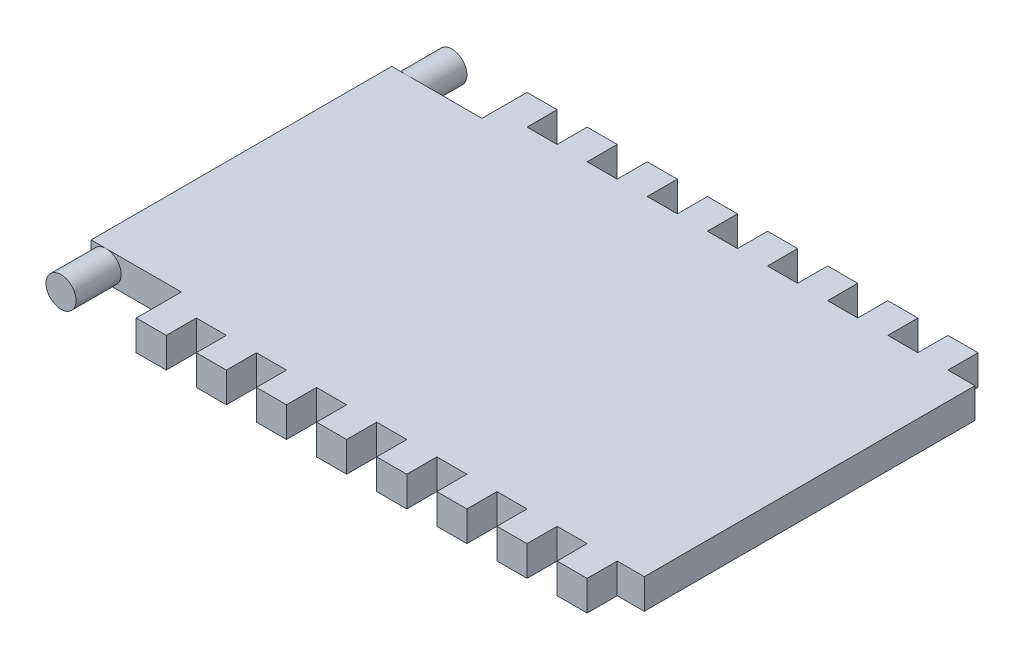
SolidWorks part; units mm, degrees
ref_plane "Plan de face" through (0, 0, 0) normal (0, 0, 1) x (1, 0, 0)
ref_plane "Plan de dessus" through (0, 0, 0) normal (0, 1, 0) x (1, 0, 0)
ref_plane "Plan de droite" through (0, 0, 0) normal (1, 0, 0) x (0, 0, -1)
sketch "Esquisse1" plane through (0, 0, 0) normal (0, 1, 0) x (1, 0, 0)
  line L1 (0, 0) -> (-189, 0)
  line L2 (0, 0) -> (0, 130)
  line L3 (0, 130) -> (-189, 130)
  line L4 (-189, 0) -> (-189, 130)
  dimension "D1" = 189
  dimension "D2" = 130
extrude "Boss.-Extru.1" add sketch "Esquisse1" along normal blind 10
sketch "Esquisse2" plane through (0, 10, 0) normal (0, 1, 0) x (1, 0, 0)
  line L1 (-189, 130) -> (-159, 130)
  line L2 (-189, 130) -> (-189, 115)
  line L3 (-189, 115) -> (-159, 115)
  line L4 (-159, 130) -> (-159, 115)
  line L5 (-189, 0) -> (-159, 0)
  line L6 (-189, 0) -> (-189, 15)
  line L7 (-189, 15) -> (-159, 15)
  line L8 (-159, 0) -> (-159, 15)
  dimension "D1" = 15
  dimension "D2" = 15
  dimension "D3" = 30
  dimension "D4" = 30
extrude "Enlèv. mat.-Extru.1" cut sketch "Esquisse2" against normal blind 10
sketch "Esquisse3" plane through (0, 10, 0) normal (0, 1, 0) x (1, 0, 0)
  line L0 (0, 130) -> (-159, 130) construction
  line L1 (-149, 130) -> (-139, 130)
  line L2 (-149, 130) -> (-149, 120)
  line L3 (-149, 120) -> (-139, 120)
  line L4 (-139, 130) -> (-139, 120)
  line L5 (-159, 115) -> (-159, 130) construction
  line L6 (-159, 0) -> (0, 0) construction
  line L7 (-149, 0) -> (-139, 0)
  line L8 (-149, 0) -> (-149, 10)
  line L9 (-149, 10) -> (-139, 10)
  line L10 (-139, 0) -> (-139, 10)
  line L11 (-159, 0) -> (-159, 15) construction
  dimension "D1" = 10
  dimension "D2" = 10
  dimension "D3" = 10
  dimension "D4" = 10
  dimension "D5" = 10
  dimension "D6" = 10
extrude "Enlèv. mat.-Extru.2" cut sketch "Esquisse3" against normal blind 10
pattern_linear "Répétition linéaire1" count 8 spacing 20 along (1, 0, 0) of "Enlèv. mat.-Extru.2"
sketch "Esquisse4" plane through (0, 0, -15) normal (0, 0, 1) x (1, 0, 0)
  line L0 (-159, 10) -> (-189, 10) construction
  line L1 (-189, 0) -> (-189, 10) construction
  line L2 (-159, 0) -> (-189, 0) construction
  circle A0 centre (-184, 5) radius 5
extrude "Boss.-Extru.2" add sketch "Esquisse4" along normal blind 15
sketch "Esquisse5" plane through (0, 0, -115) normal (0, 0, -1) x (-1, 0, 0)
  line L0 (189, 0) -> (159, 0) construction
  line L1 (189, 10) -> (159, 10) construction
  line L2 (189, 0) -> (189, 10) construction
  circle A0 centre (184, 5) radius 5
extrude "Boss.-Extru.4" add sketch "Esquisse5" along normal blind 15
